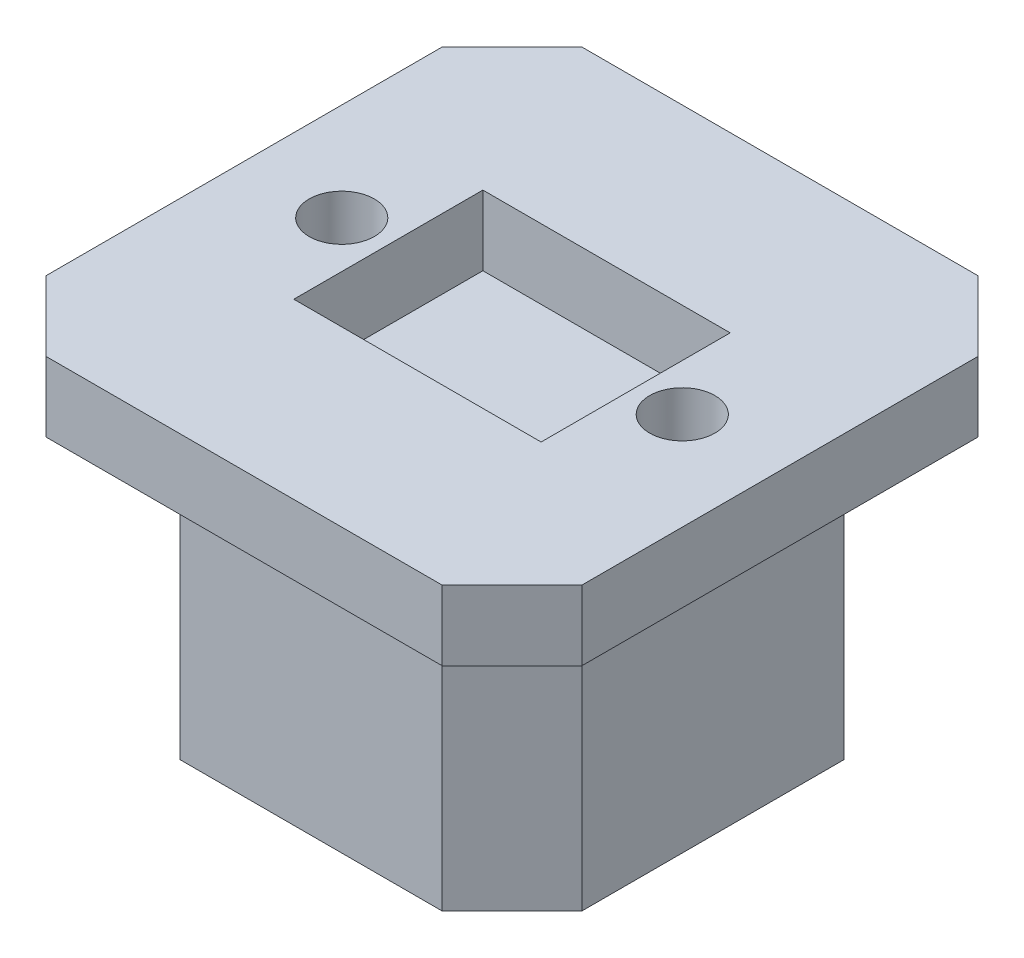
SolidWorks part; units mm, degrees
ref_plane "Front" through (0, 0, 0) normal (0, 0, 1) x (1, 0, 0)
ref_plane "Top" through (0, 0, 0) normal (0, 1, 0) x (1, 0, 0)
ref_plane "Right" through (0, 0, 0) normal (1, 0, 0) x (0, 0, -1)
sketch "Sketch1" plane through (0, 0, 0) normal (0, 1, 0) x (1, 0, 0)
  line L1 (-19.1751, -19.1751) -> (19.1751, -19.1751)
  line L2 (-19.1751, -19.1751) -> (-19.1751, 19.1751)
  line L3 (-19.1751, 19.1751) -> (19.1751, 19.1751)
  line L4 (19.1751, -19.1751) -> (19.1751, 19.1751)
  line L5 (-19.1751, -19.1751) -> (19.1751, 19.1751) construction
  line L6 (-19.1751, 19.1751) -> (19.1751, -19.1751) construction
  point P0 (0, 0)
extrude "Boss-Extrude1" add sketch "Sketch1" along normal blind 5
sketch "Sketch2" plane through (0, 0, 0) normal (0, 1, 0) x (1, 0, 0)
  line L0 (-19.1751, -19.1751) -> (19.1751, -19.1751) construction
  line L1 (-14.3751, -14.3751) -> (14.3751, -14.3751)
  line L2 (-14.3751, -14.3751) -> (-14.3751, 14.3751)
  line L3 (-14.3751, 14.3751) -> (14.3751, 14.3751)
  line L4 (14.3751, -14.3751) -> (14.3751, 14.3751)
  line L5 (-14.3751, -14.3751) -> (14.3751, 14.3751) construction
  line L6 (-14.3751, 14.3751) -> (14.3751, -14.3751) construction
  point P0 (0, 0)
  dimension "D1" = 4.8
extrude "Boss-Extrude2" add sketch "Sketch2" against normal blind 20
chamfer "Chamfer1" distance 5 angle 45 8 edges at (19.1751, 2.5, 19.1751) (19.1751, 2.5, -19.1751) (-19.1751, 2.5, -19.1751) (-19.1751, 2.5, 19.1751) (-14.3751, -10, 14.3751) (-14.3751, -10, -14.3751) (14.3751, -10, -14.3751) (14.3751, -10, 14.3751)
sketch "Sketch3" plane through (0, 5, 0) normal (0, 1, 0) x (1, 0, 0)
  line L0 (19.1751, 0) -> (-19.1751, 0) construction
  line L1 (8.8496, 6.7657) -> (-8.8496, 6.7657)
  line L2 (8.8496, 6.7657) -> (8.8496, -6.7657)
  line L3 (8.8496, -6.7657) -> (-8.8496, -6.7657)
  line L4 (-8.8496, 6.7657) -> (-8.8496, -6.7657)
  line L5 (8.8496, 6.7657) -> (-8.8496, -6.7657) construction
  line L6 (8.8496, -6.7657) -> (-8.8496, 6.7657) construction
  line L7 (19.1751, -14.1751) -> (19.1751, 14.1751) construction
  line L8 (-19.1751, 14.1751) -> (-19.1751, -14.1751) construction
  line L9 (0, -19.1751) -> (0, 19.1751) construction
  line L10 (-14.1751, -19.1751) -> (14.1751, -19.1751) construction
  line L11 (14.1751, 19.1751) -> (-14.1751, 19.1751) construction
  line L12 (8.8496, -6.7657) -> (8.8496, 6.7657) construction
  line L13 (-8.8496, -10.5) -> (8.8496, -10.5) construction
  line L14 (-12.1848, 0) -> (-12.1848, -13.7576) construction
  line L15 (-12.1848, -13.7576) -> (12.1848, -13.7576) construction
  line L16 (12.1848, -13.7576) -> (12.1848, 0.5472) construction
  circle A0 centre (-12.1848, 0) radius 2.3327
  circle A1 centre (12.1848, 0) radius 2.3327
  circle A2 centre (12.1848, 0) radius 2.3327 construction
  point P0 (0, 0)
extrude "Cut-Extrude1" cut sketch "Sketch3" against normal up to surface (5 mm away) up to face at (0, 0, 0)
sketch "Sketch4" plane through (0, -20, 0) normal (0, -1, 0) x (1, 0, 0)
  circle A0 centre (0, 0) radius 4.3192
extrude "Cut-Extrude2" cut sketch "Sketch4" against normal blind 9
